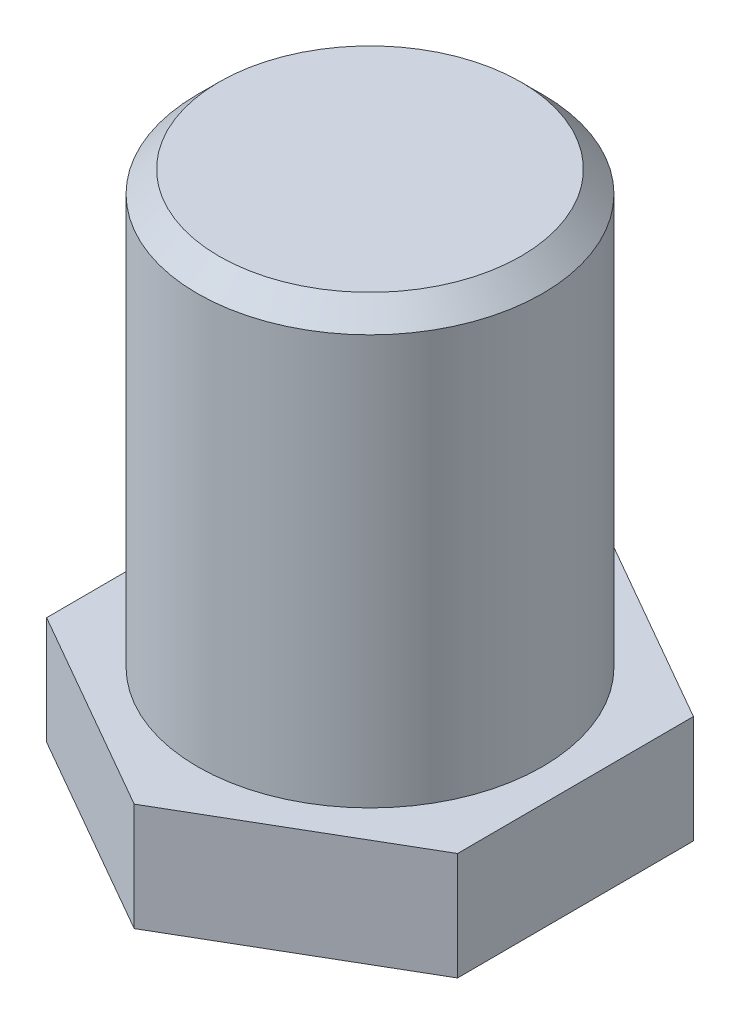
SolidWorks part; units mm, degrees
ref_plane "Front Plane" through (0, 0, 0) normal (0, 0, 1) x (1, 0, 0)
ref_plane "Top Plane" through (0, 0, 0) normal (0, 1, 0) x (1, 0, 0)
ref_plane "Right Plane" through (0, 0, 0) normal (1, 0, 0) x (0, 0, -1)
sketch "Sketch1" plane through (0, 0, 0) normal (0, 1, 0) x (1, 0, 0)
  line L1 (9.5172, -5.455) -> (9.4827, 5.5146)
  line L2 (9.4827, 5.5146) -> (-0.0344, 10.9696)
  line L3 (-0.0344, 10.9696) -> (-9.5172, 5.455)
  line L4 (-9.5172, 5.455) -> (-9.4827, -5.5146)
  line L5 (-9.4827, -5.5146) -> (0.0344, -10.9696)
  line L6 (0.0344, -10.9696) -> (9.5172, -5.455)
  circle A0 centre (0, 0) radius 9.5 construction
  dimension "D1" = 19
extrude "Boss-Extrude1" add sketch "Sketch1" along normal blind 5
sketch "Sketch2" plane through (0, 0, 0) normal (0, 1, 0) x (1, 0, 0)
  circle A0 centre (0, 0) radius 8
  dimension "D1" = 16
extrude "Boss-Extrude2" add sketch "Sketch2" along normal blind 25
chamfer "Chamfer1" distance 1 angle 45 1 edges at (0, 25, 8)
